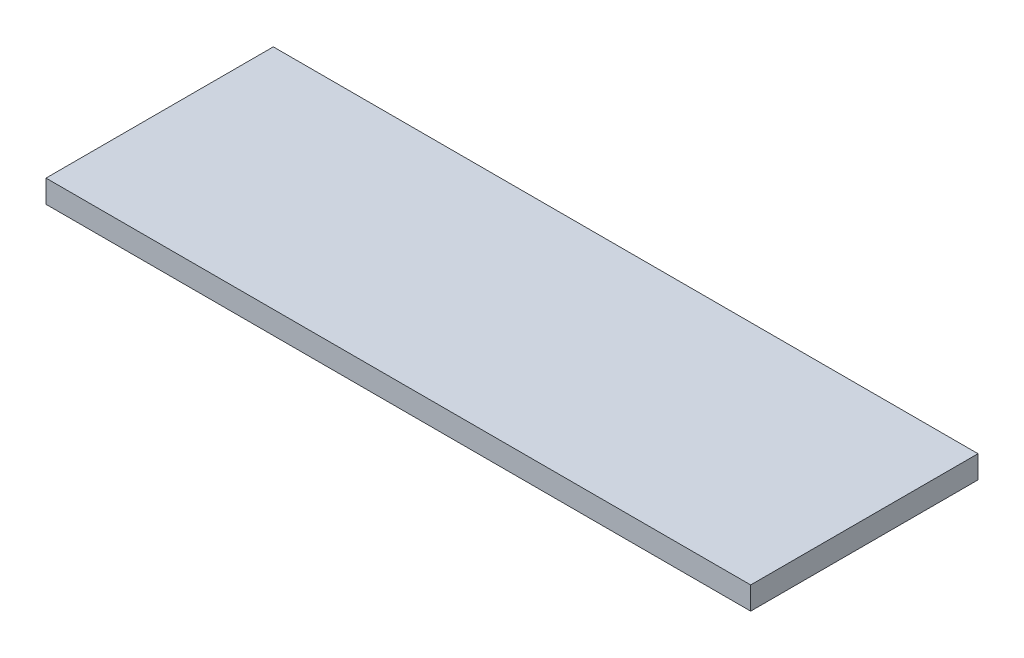
SolidWorks part; units mm, degrees
ref_plane "Front Plane" through (0, 0, 0) normal (0, 0, 1) x (1, 0, 0)
ref_plane "Top Plane" through (0, 0, 0) normal (0, 1, 0) x (1, 0, 0)
ref_plane "Right Plane" through (0, 0, 0) normal (1, 0, 0) x (0, 0, -1)
sketch "Sketch1" plane through (0, 0, 0) normal (0, 1, 0) x (1, 0, 0)
  line L0 (-155, 50) -> (155, -50) construction
  line L1 (-155, 50) -> (155, 50)
  line L2 (-155, 50) -> (-155, -50)
  line L3 (-155, -50) -> (155, -50)
  line L4 (155, 50) -> (155, -50)
  dimension "D1" = 310
  dimension "D2" = 100
extrude "Boss-Extrude1" add sketch "Sketch1" along normal blind 10
